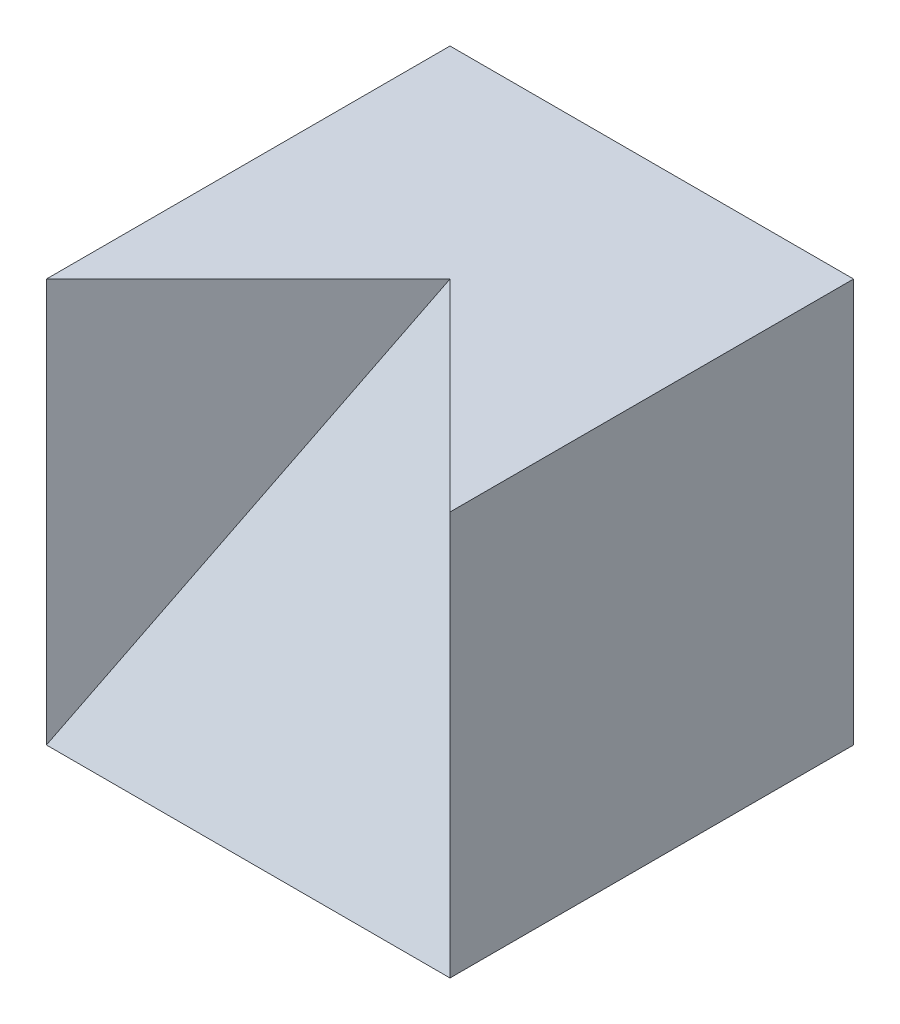
SolidWorks part; units mm, degrees
ref_plane "Front" through (0, 0, 0) normal (0, 0, 1) x (1, 0, 0)
ref_plane "Top" through (0, 0, 0) normal (0, 1, 0) x (1, 0, 0)
ref_plane "Right" through (0, 0, 0) normal (1, 0, 0) x (0, 0, -1)
sketch "Sketch2" plane through (0, 0, 0) normal (0, 1, 0) x (1, 0, 0)
  line L1 (-2, -2) -> (2, -2)
  line L2 (-2, -2) -> (-2, 2)
  line L3 (-2, 2) -> (2, 2)
  line L4 (2, -2) -> (2, 2)
  line L5 (-2, -2) -> (2, 2) construction
  line L6 (-2, 2) -> (2, -2) construction
  point P0 (0, 0)
  dimension "D1" = 4
  dimension "D2" = 4
extrude "Boss-Extrude1" add sketch "Sketch2" along normal blind 4
sketch3d "3DSketch1"
  line L0 (2, 4, -2) -> (-2, 4, -2) construction
  line L1 (2, 4, 2) -> (2, 4, -2) construction
  line L2 (2, 0, 2) -> (0, 4, 0)
  line L3 (0, 4, 0) -> (-2, 0, 2)
  line L4 (-2, 0, 2) -> (2, 0, 2)
  point P0 (0, 4, 0)
  dimension "D1" = 2
  dimension "D2" = 2
extrude "Cut-Extrude1" cut sketch "3DSketch1" along direction (0, -1, 0) on the side of the normal blind 4
